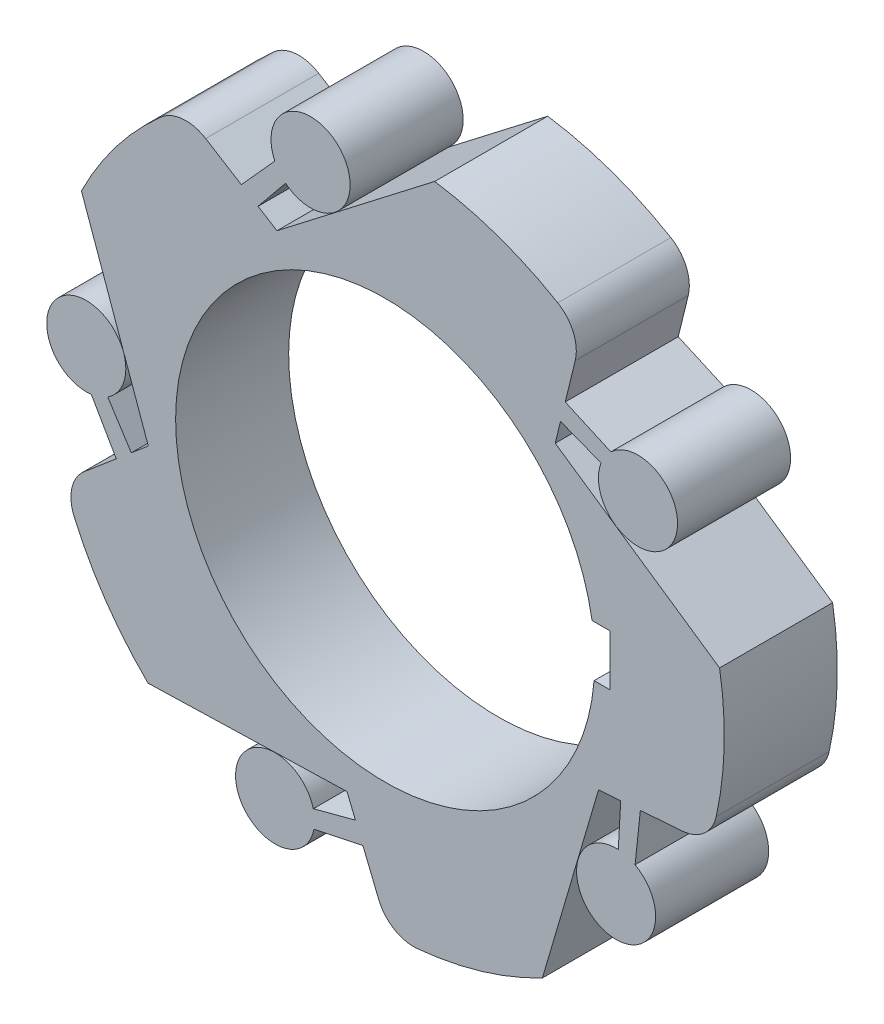
SolidWorks part; units mm, degrees
ref_plane "Front Plane" through (0, 0, 0) normal (0, 0, 1) x (1, 0, 0)
ref_plane "Top Plane" through (0, 0, 0) normal (0, 1, 0) x (1, 0, 0)
ref_plane "Right Plane" through (0, 0, 0) normal (1, 0, 0) x (0, 0, -1)
sketch "Sketch1" plane through (0, 0, 0) normal (0, 0, 1) x (1, 0, 0)
  line L0 (0, 55.4898) -> (0, -59.6128)
  circle A0 centre (0, 0) radius 90
  dimension "D1" = 180
extrude "Boss-Extrude1" add sketch "Sketch1" along normal blind 30
sketch "Sketch4" plane through (0, 0, 0) normal (0, 0, 1) x (1, 0, 0)
  line L0 (-80.6222, 40.0007) -> (-62.8792, -9.7785)
  line L1 (-71.6642, 35.5562) -> (-71.6642, 35.5562)
  line L2 (-62.8792, -9.7785) -> (-85.2933, -28.7238)
  line L3 (13.1293, 89.0372) -> (-28.7306, 56.78)
  line L4 (-28.7306, 56.78) -> (-53.675, 72.2426)
  line L5 (88.7366, 15.0273) -> (45.1227, 44.8704)
  line L6 (45.1227, 44.8704) -> (52.1203, 73.3722)
  line L7 (41.7129, -79.7498) -> (56.618, -29.0485)
  line L8 (56.618, -29.0485) -> (85.8871, -26.8961)
  line L9 (-62.9566, -64.3154) -> (-10.1309, -62.8234)
  line L10 (-10.1309, -62.8234) -> (0.9609, -89.9949)
  arc A0 (-80.6222, 40.0007) -> (-85.2933, -28.7238) centre (0, 0) ccw
  circle A1 centre (0, 0) radius 90 construction
  arc A2 (13.1293, 89.0372) -> (-53.675, 72.2426) centre (0, 0) ccw
  arc A3 (88.7366, 15.0273) -> (52.1203, 73.3722) centre (0, 0) ccw
  arc A4 (41.7129, -79.7498) -> (85.8871, -26.8961) centre (0, 0) ccw
  arc A5 (-62.9566, -64.3154) -> (0.9609, -89.9949) centre (0, 0) ccw
  point P23 (0, 0)
  dimension "D1" = 5
extrude "Cut-Extrude4" cut sketch "Sketch4" along normal blind 30 contours L5 A3 L6 | L7 A4 L8 | L9 A5 L10 | L0 A0 L2 | L3 A2 L4
sketch "Sketch5" plane through (0, 0, 0) normal (0, 0, 1) x (1, 0, 0)
  circle A0 centre (0, 0) radius 55.626
extrude "Cut-Extrude5" cut sketch "Sketch5" along normal blind 30
sketch "Sketch6" plane through (0, 0, 0) normal (0, 0, 1) x (1, 0, 0)
  line L1 (59.7237, -4.5415) -> (52.337, -4.5415)
  line L2 (59.7237, -4.5415) -> (59.7237, 9.0008)
  line L3 (59.7237, 9.0008) -> (52.337, 9.0008)
  line L4 (52.337, -4.5415) -> (52.337, 9.0008)
extrude "Cut-Extrude6" cut sketch "Sketch6" along normal blind 30
fillet "Fillet1" radius 10 5 edges at (85.8871, -26.8961, 15) (0.9609, -89.9949, 15) (-85.2933, -28.7238, 15) (-53.675, 72.2426, 15) (52.1203, 73.3722, 15)
sketch "Sketch8" plane through (0, 0, 30) normal (0, 0, 1) x (1, 0, 0)
  circle A0 centre (0, 0) radius 90
  circle A1 centre (-19.8084, 76.9825) radius 10.4981
  circle A2 centre (67.0936, 42.6278) radius 10.4981
  circle A3 centre (61.2745, -50.6371) radius 10.4981
  circle A4 centre (-29.2239, -73.9232) radius 10.4981
  circle A5 centre (-79.3358, 4.95) radius 10.4981
  point P16 (0, 0)
  dimension "D1" = 5
extrude "Boss-Extrude2" add sketch "Sketch8" against normal blind 30 separate body contours A2 | A3 | A4 | A5 | A1
sketch "Sketch9" plane through (0, 0, 0) normal (0, 0, 1) x (1, 0, 0)
  line L0 (-29.2984, 72.4936) -> (-38.1865, 62.6415)
  line L1 (-28.7306, 56.78) -> (-47.6423, 68.503) construction
  line L2 (-33.7425, 59.8867) -> (-26.441, 68.845)
  line L3 (-33.7425, 59.8867) -> (-38.1865, 62.6415)
  line L4 (46.5287, 50.597) -> (57.3047, 46.4211)
  line L5 (59.8918, 50.2662) -> (47.7753, 55.6748)
  line L6 (46.5287, 50.597) -> (47.7753, 55.6748)
  line L7 (62.4988, -28.6161) -> (61.8572, -40.1551)
  line L8 (66.3136, -41.4274) -> (67.7132, -28.2326)
  line L9 (62.4988, -28.6161) -> (67.7132, -28.2326)
  line L10 (-7.9023, -68.2827) -> (-19.0749, -71.2383)
  line L11 (-18.9078, -75.8698) -> (-5.9263, -73.1235)
  line L12 (-7.9023, -68.2827) -> (-5.9263, -73.1235)
  line L13 (-67.3827, -13.585) -> (-73.6461, -3.8726)
  line L14 (-77.9993, -5.4627) -> (-71.3759, -16.9602)
  line L15 (-67.3827, -13.585) -> (-71.3759, -16.9602)
  circle A0 centre (-19.8084, 76.9825) radius 10.4981 construction
  arc A1 (-29.2984, 72.4936) -> (-26.441, 68.845) centre (-19.8084, 76.9825) ccw
  arc A2 (59.8918, 50.2662) -> (57.3047, 46.4211) centre (67.0936, 42.6278) ccw
  arc A3 (66.3136, -41.4274) -> (61.8572, -40.1551) centre (61.2745, -50.6371) ccw
  arc A4 (-18.9078, -75.8698) -> (-19.0749, -71.2383) centre (-29.2239, -73.9232) ccw
  arc A5 (-77.9993, -5.4627) -> (-73.6461, -3.8726) centre (-79.3358, 4.95) ccw
  point P33 (0, 0)
  dimension "D1" = 5
extrude "Boss-Extrude4" add sketch "Sketch9" along normal blind 30
